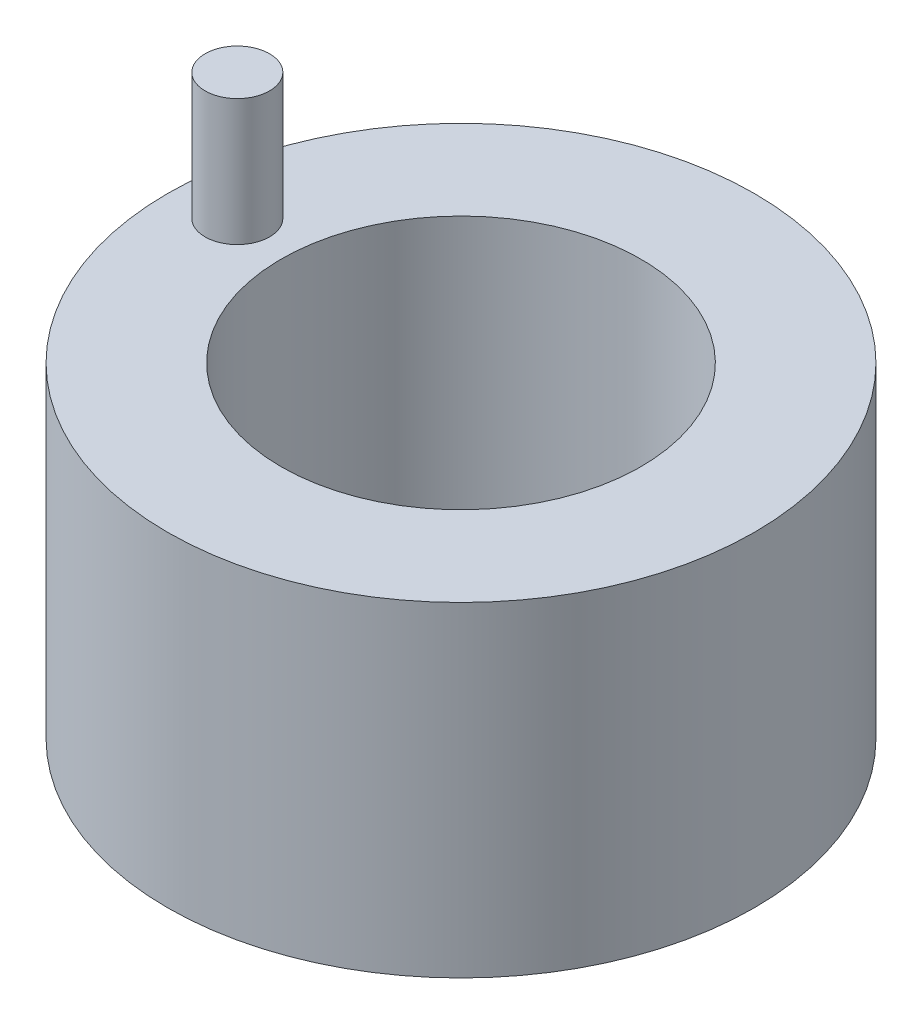
SolidWorks part; units mm, degrees
ref_plane "Front Plane" through (0, 0, 0) normal (0, 0, 1) x (1, 0, 0)
ref_plane "Top Plane" through (0, 0, 0) normal (0, 1, 0) x (1, 0, 0)
ref_plane "Right Plane" through (0, 0, 0) normal (1, 0, 0) x (0, 0, -1)
sketch "Sketch1" plane through (0, 0, 0) normal (0, 1, 0) x (1, 0, 0)
  circle A0 centre (0, 0) radius 64.9649
extrude "Boss-Extrude1" add sketch "Sketch1" along normal blind 72
sketch "Sketch2" plane through (0, 72, 0) normal (0, 1, 0) x (1, 0, 0)
  circle A0 centre (0, 0) radius 39.8269
extrude "Cut-Extrude1" cut sketch "Sketch2" against normal blind 72
sketch "Sketch3" plane through (0, 72, 0) normal (0, 1, 0) x (1, 0, 0)
  circle A0 centre (-52.4782, 2.9566) radius 7.1327
extrude "Boss-Extrude2" add sketch "Sketch3" along normal blind 28
